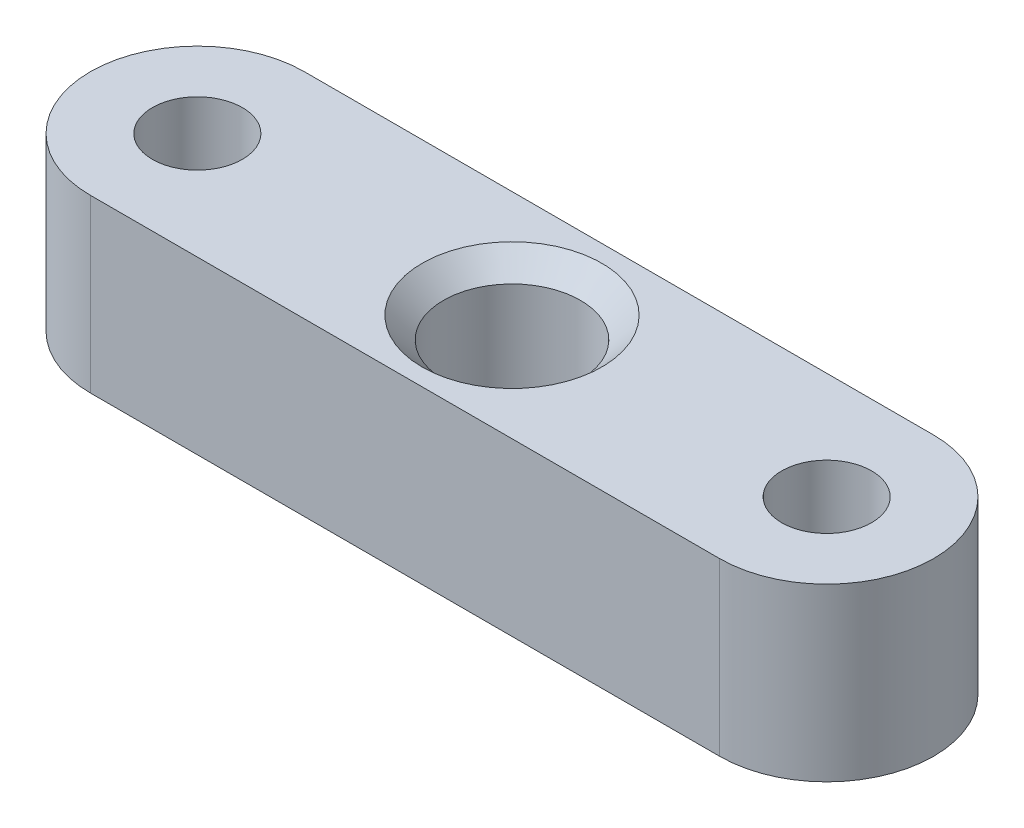
SolidWorks part; units mm, degrees
ref_plane "Front Plane" through (0, 0, 0) normal (0, 0, 1) x (1, 0, 0)
ref_plane "Top Plane" through (0, 0, 0) normal (0, 1, 0) x (1, 0, 0)
ref_plane "Right Plane" through (0, 0, 0) normal (1, 0, 0) x (0, 0, -1)
sketch "Sketch1" plane through (0, 0, 0) normal (0, 1, 0) x (1, 0, 0)
  line L0 (-14.7, 0) -> (14.7, 0) construction
  line L1 (-14.7, 5) -> (14.7, 5)
  line L2 (-14.7, -5) -> (14.7, -5)
  arc A0 (-14.7, 5) -> (-14.7, -5) centre (-14.7, 0) ccw
  arc A1 (14.7, -5) -> (14.7, 5) centre (14.7, 0) ccw
  circle A2 centre (-14.7, 0) radius 2.1
  circle A3 centre (14.7, 0) radius 2.1
  circle A4 centre (0, 0) radius 3.2
  point P2 (0, 0)
  dimension "D3" = 4.2
  dimension "D4" = 4.2
  dimension "D5" = 6.4
  dimension "D1" = 10
  dimension "D2" = 29.4
extrude "Boss-Extrude1" add sketch "Sketch1" along normal blind 8
sketch "Sketch2" plane through (0, 8, 0) normal (0, 1, 0) x (1, 0, 0)
  line L2 (14.7, 5) -> (-14.7, 5)
  line L3 (-14.7, -5) -> (14.7, -5)
  line L4 (14.7, 5) -> (-14.7, 5)
  line L5 (-14.7, -5) -> (14.7, -5)
  circle A1 centre (0, 0) radius 3.2
  circle A2 centre (0, 0) radius 3.2
  circle A3 centre (14.7, 0) radius 2.1
  circle A4 centre (14.7, 0) radius 2.1
  circle A5 centre (-14.7, 0) radius 2.1
  circle A6 centre (-14.7, 0) radius 2.1
  arc A8 (14.7, -5) -> (14.7, 5) centre (14.7, 0) ccw
  arc A9 (-14.7, 5) -> (-14.7, -5) centre (-14.7, 0) ccw
  arc A10 (14.7, -5) -> (14.7, 5) centre (14.7, 0) ccw
  arc A11 (-14.7, 5) -> (-14.7, -5) centre (-14.7, 0) ccw
  dimension "D1" = 0
  dimension "D2" = 0
  dimension "D3" = 0
  dimension "D4" = 0
extrude "Cut-Extrude1" cut sketch "Sketch2" against normal blind 6 contours A2
sketch "Sketch3" plane through (0, 0, 0) normal (0, -1, 0) x (1, 0, 0)
  circle A0 centre (0, 0) radius 2
  dimension "D1" = 4
extrude "Cut-Extrude2" cut sketch "Sketch3" against normal blind 6
chamfer "Chamfer1" distance 1 angle 45 1 edges at (0, 8, 3.2)
equation "\"D2@Sketch1\"=33.4-4"
equation "\"D4@Sketch1\"=\"D3@Sketch1\""
